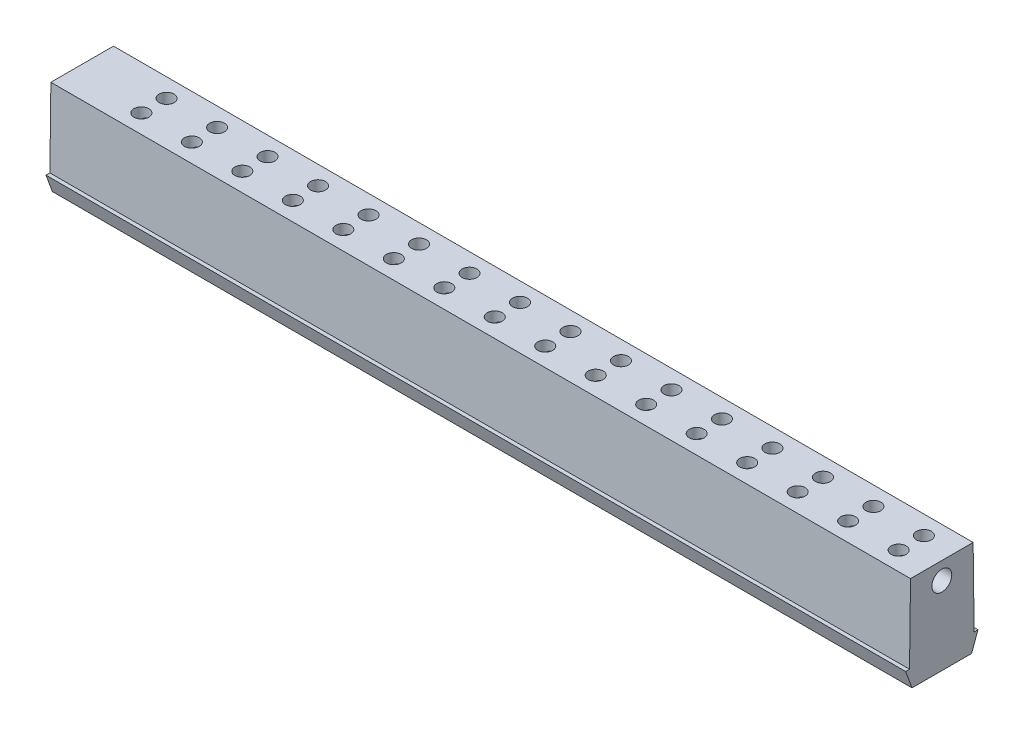
SolidWorks part; units mm, degrees
material "ABS PC"
ref_plane "Front Plane" through (0, 0, 0) normal (0, 0, 1) x (1, 0, 0)
ref_plane "Top Plane" through (0, 0, 0) normal (0, 1, 0) x (1, 0, 0)
ref_plane "Right Plane" through (0, 0, 0) normal (1, 0, 0) x (0, 0, -1)
sketch "Sketch1" plane through (0, 0, 0) normal (1, 0, 0) x (0, 0, -1)
  line L0 (-3, 0) -> (3, 0)
  line L1 (3, 0) -> (3.64, 1.75)
  line L2 (3.15, 9.6) -> (-3.15, 9.6)
  line L3 (-3.15, 9.6) -> (-3.25, 1.75)
  line L4 (3.64, 1.75) -> (3.25, 1.75)
  line L5 (-3.64, 1.75) -> (-3, 0)
  line L6 (0, 0) -> (0, 9.6) construction
  line L7 (-3.25, 1.75) -> (-3.64, 1.75)
  line L8 (3.25, 1.75) -> (3.15, 9.6)
  dimension "D1" = 7.28
  dimension "D2" = 9.6
  dimension "D3" = 6
  dimension "D4" = 6.3
  dimension "D5" = 1.75
  dimension "D6" = 6.5
  dimension "D7" = 1.46
extrude "Boss-Extrude1" add sketch "Sketch1" along normal blind 86.5
sketch "Sketch2" plane through (86.5, 0, 0) normal (-1, 0, 0) x (0, 0, 1)
  line L1 (-3.15, 9.6) -> (3.15, 9.6) construction
  circle A0 centre (0, 7.85) radius 1
  dimension "D2" = 2
  dimension "D1" = 0.75
extrude "Cut-Extrude1" cut sketch "Sketch2" along normal offset from surface (84 mm away) 2.5 up to face at (0, 3.275, 0)
sketch "Sketch3" plane through (0, 0, 0) normal (0, -1, 0) x (1, 0, 0)
  circle A14 centre (83.425, 1.27) radius 0.9144
  circle A15 centre (78.345, -1.27) radius 0.9144
  circle A16 centre (73.265, 1.27) radius 0.9144
  circle A17 centre (68.185, -1.27) radius 0.9144
  circle A18 centre (58.025, -1.27) radius 0.9144
  circle A19 centre (52.945, 1.27) radius 0.9144
  circle A20 centre (47.865, -1.27) radius 0.9144
  circle A21 centre (37.705, -1.27) radius 0.9144
  circle A22 centre (32.625, 1.27) radius 0.9144
  circle A23 centre (27.545, -1.27) radius 0.9144
  circle A24 centre (22.465, 1.27) radius 0.9144
  circle A25 centre (17.385, -1.27) radius 0.9144
  circle A26 centre (12.305, 1.27) radius 0.9144
  circle A27 centre (7.225, -1.27) radius 0.9144
  circle A29 centre (63.105, 1.27) radius 0.9144
  circle A30 centre (42.785, 1.27) radius 0.9144
  dimension "D1" = 1.8288
extrude "Cut-Extrude2" cut sketch "Sketch3" against normal blind 5.207
sketch "Sketch4" plane through (0, 9.6, 0) normal (0, 1, 0) x (1, 0, 0)
  line L0 (7.225, -1.27) -> (7.225, 1.27) construction
  line L1 (7.225, 0) -> (0, 0) construction
  line L2 (0, 3.15) -> (0, -3.15) construction
  circle A0 centre (7.225, 1.27) radius 0.75
  circle A1 centre (7.225, -1.27) radius 0.75
  circle A2 centre (7.225, 1.27) radius 0.9144 construction
  dimension "D1" = 1.5
extrude "Cut-Extrude3" cut sketch "Sketch4" against normal blind 5.08
pattern_linear "LPattern1" count 16 spacing 5.08 along (1, 0, 0) of "Cut-Extrude3"
ref_point "Point1"
